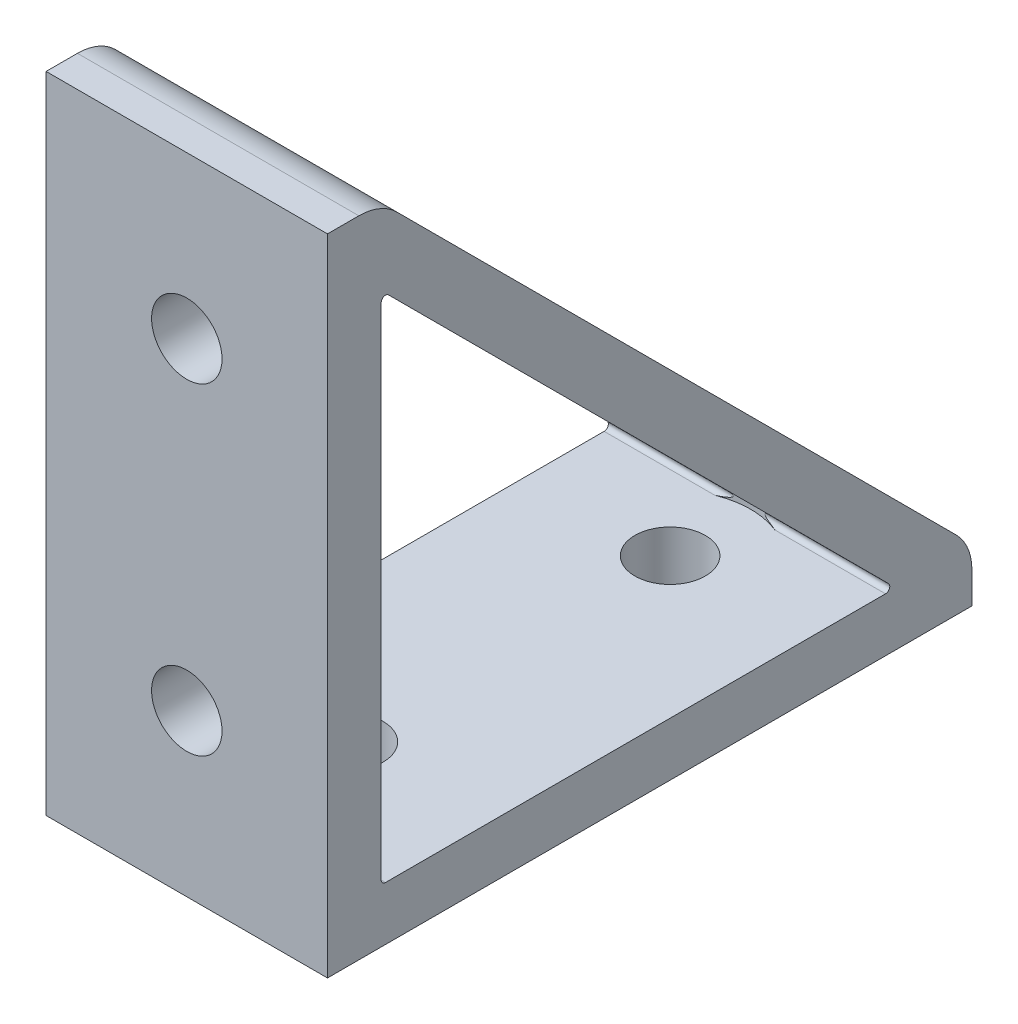
SolidWorks part; units mm, degrees
ref_plane "Front"
ref_plane "Top" through (0, 0, 0) normal (0, 1, 0) x (1, 0, 0)
ref_plane "Right" through (0, 0, 0) normal (1, 0, 0) x (0, 0, -1)
sketch "Sketch1" plane through (0, 0, 0) normal (1, 0, 0) x (0, 0, -1)
  line L0 (36.7792, 36.7792) -> (41.2693, 41.2693) construction
  line L1 (6.35, 38.1) -> (0, 38.1) construction
  line L2 (36.42, 6.35) -> (36.42, 0) construction
  line L8 (0, 76.2) -> (0, 0)
  line L9 (0, 0) -> (76.2, 0)
  line L10 (76.2, 0) -> (76.2, 3.7084)
  line L11 (6.35, 65.982) -> (6.35, 6.858)
  line L12 (6.858, 6.35) -> (65.982, 6.35)
  line L13 (3.7084, 76.2) -> (0, 76.2)
  line L14 (8.1985, 74.3401) -> (74.3401, 8.1985)
  line L15 (7.2172, 66.3412) -> (66.3412, 7.2172)
  arc A0 (6.35, 6.858) -> (6.858, 6.35) centre (6.858, 6.858) ccw
  arc A1 (65.982, 6.35) -> (66.3412, 7.2172) centre (65.982, 6.858) ccw
  arc A2 (7.2172, 66.3412) -> (6.35, 65.982) centre (6.858, 65.982) ccw
  arc A3 (8.1985, 74.3401) -> (3.7084, 76.2) centre (3.7084, 69.85) ccw
  arc A4 (76.2, 3.7084) -> (74.3401, 8.1985) centre (69.85, 3.7084) ccw
  dimension "OuterRadius" = 6.35
  dimension "InnerRadius" = 0.508
  dimension "LengthZ" = 76.2
  dimension "HeightY" = 76.2
  dimension "Thickness" = 6.35
  dimension "Angle" = 45
  dimension "CornerZ" = 3.7084
extrude "Base Extrude" add sketch "Sketch1" against normal blind 33.274
sketch "Sketch2" plane through (0, 0, 0) normal (0, -1, 0) x (1, 0, 0)
  line L1 (-33.274, 0) -> (0, 0) construction
  line L2 (0, 0) -> (0, -76.2) construction
  circle A0 centre (-16.637, -19.05) radius 4.1656
  dimension "D1" = 8.3312
  dimension "Hole1Z" = 19.05
  dimension "Hole1X" = 16.637
extrude "Hole1" cut sketch "Sketch2" against normal up to next
sketch "Sketch3" plane through (0, 6.35, 0) normal (0, 1, 0) x (-1, 0, 0)
  circle A0 centre (16.637, -19.05) radius 9.525
  dimension "Hole1aDiam" = 19.05
extrude "Hole1a" cut sketch "Sketch3" along normal through all
pattern_linear "Hole1 Pattern" count 2 spacing 38.1 along (0, 0, -1) of "Hole1", "Hole1a"
sketch "Sketch4" plane through (0, 0, 0) normal (0, 0, 1) x (1, 0, 0)
  line L1 (0, 76.2) -> (0, 0) construction
  line L2 (-33.274, 0) -> (0, 0) construction
  circle A0 centre (-16.637, 19.05) radius 4.1656
  dimension "Hole2Diam" = 8.3312
  dimension "Hole2X" = 16.637
  dimension "Hole2Y" = 19.05
extrude "Hole2" cut sketch "Sketch4" against normal up to next
sketch "Sketch5" plane through (0, 0, -6.35) normal (0, 0, -1) x (-1, 0, 0)
  circle A0 centre (16.637, 19.05) radius 9.525
  dimension "Hole2aDiam" = 19.05
extrude "Hole2a" cut sketch "Sketch5" along normal through all
pattern_linear "Hole2 Pattern" count 2 spacing 38.1 along (0, 1, 0) of "Hole2", "Hole2a"
ref_plane "Mate 1" through (0, 0, 0) normal (0, -1, 0) x (1, 0, 0)
ref_plane "Mate 2"
ref_plane "Mate 3" through (-16.637, 0, 0) normal (-1, 0, 0) x (0, 0, 1)
ref_plane "Mate 4"
ref_plane "Mate 5"
ref_plane "Mate 6"
